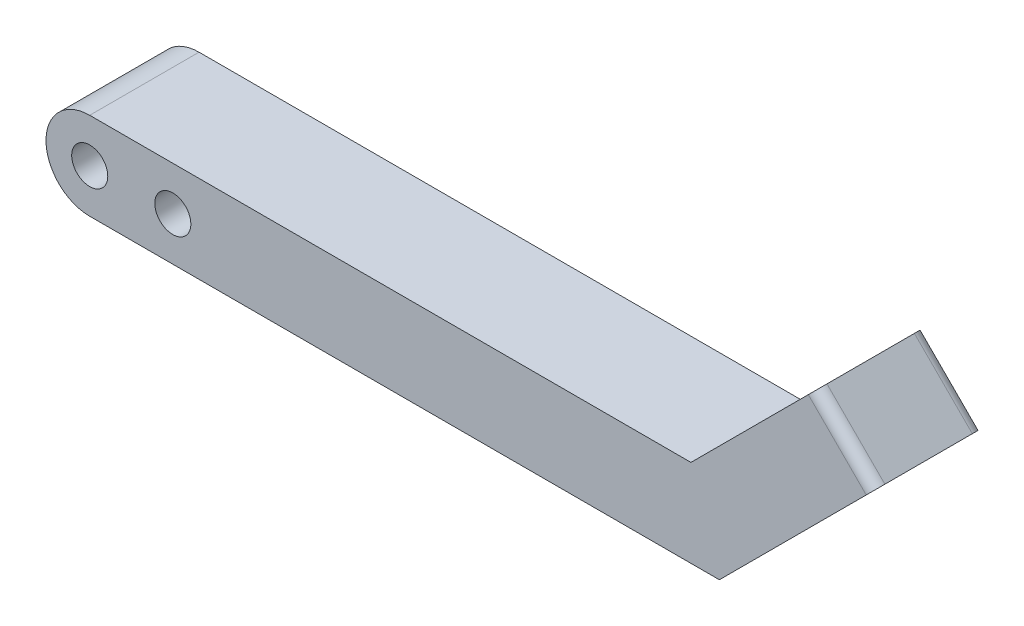
SolidWorks part; units mm, degrees
ref_plane "前视基准面" through (0, 0, 0) normal (0, 0, 1) x (1, 0, 0)
ref_plane "上视基准面" through (0, 0, 0) normal (0, 1, 0) x (1, 0, 0)
ref_plane "右视基准面" through (0, 0, 0) normal (1, 0, 0) x (0, 0, -1)
other "Configuration Table"
sketch "Sketch1" plane through (0, 0, 0) normal (0, 0, 1) x (1, 0, 0)
  line L0 (-42.3111, 4.1791) -> (12.6889, 4.1791)
  line L1 (-42.3111, -3.8209) -> (15.2889, -3.8209)
  line L2 (12.6889, 4.1791) -> (24.131, 15.6213)
  line L3 (15.2889, -3.8209) -> (29.431, 10.3213)
  line L4 (29.431, 10.3213) -> (24.131, 15.6213)
  circle A0 centre (-42.3111, 0.1791) radius 1.65
  circle A1 centre (-42.3111, 0.1791) radius 4
  circle A2 centre (-34.7111, 0.1791) radius 1.65
  dimension "D1" = 3.3
  dimension "D2" = 8
  dimension "D5" = 3.3
  dimension "D3" = 57.6
  dimension "D4" = 55
  dimension "D6" = 7.6
  dimension "D7" = 12.6889
  dimension "D8" = 0.1791
  dimension "D9" = 135
  dimension "D10" = 20
extrude "Boss-Extrude1" add sketch "Sketch1" along normal blind 10 contours A1 L1 L3 L4 L2 L0 A2 | A1 A0
sketch "Sketch2" plane through (4.2549, -4.2549, 0) normal (-0.7071, 0.7071, 0) x (0, 0, 1)
  line L0 (0, 20.0183) -> (10, 20.0183) construction
  line L1 (0, 11.9275) -> (0, 28.1091) construction
  line L2 (10, 11.9275) -> (10, 28.1091) construction
  line L3 (5, 28.1091) -> (5, 11.9275) construction
  line L4 (10, 28.1091) -> (0, 28.1091) construction
  line L5 (10, 11.9275) -> (0, 11.9275) construction
  circle A0 centre (5, 20.0183) radius 2
  dimension "D1" = 4
extrude "Cut-Extrude1" cut sketch "Sketch2" against normal through all
fillet "Fillet1" radius 1 2 edges at (26.781, 12.9713, 0) (26.781, 12.9713, 10)
